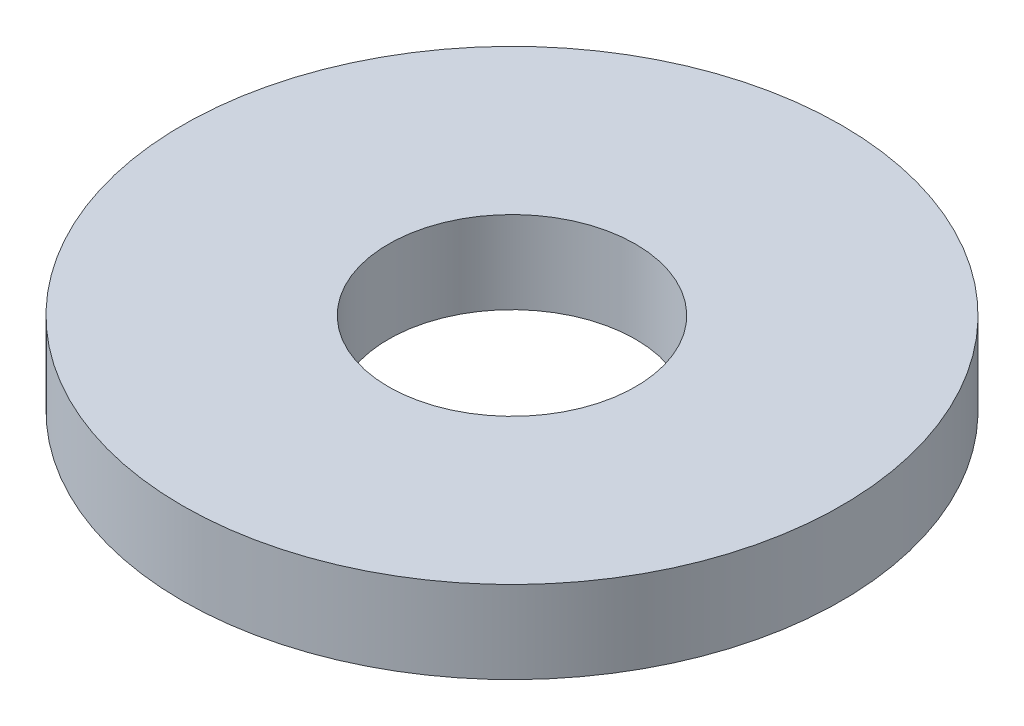
SolidWorks part; units mm, degrees
ref_plane "Front Plane" through (0, 0, 0) normal (0, 0, 1) x (1, 0, 0)
ref_plane "Top Plane" through (0, 0, 0) normal (0, 1, 0) x (1, 0, 0)
ref_plane "Right Plane" through (0, 0, 0) normal (1, 0, 0) x (0, 0, -1)
sketch "Sketch1" plane through (0, 0, 0) normal (0, 1, 0) x (1, 0, 0)
  circle A0 centre (0, 0) radius 1.5
  circle A1 centre (0, 0) radius 4
  dimension "D1" = 3
  dimension "D2" = 8
extrude "Boss-Extrude1" add sketch "Sketch1" along normal blind 1
